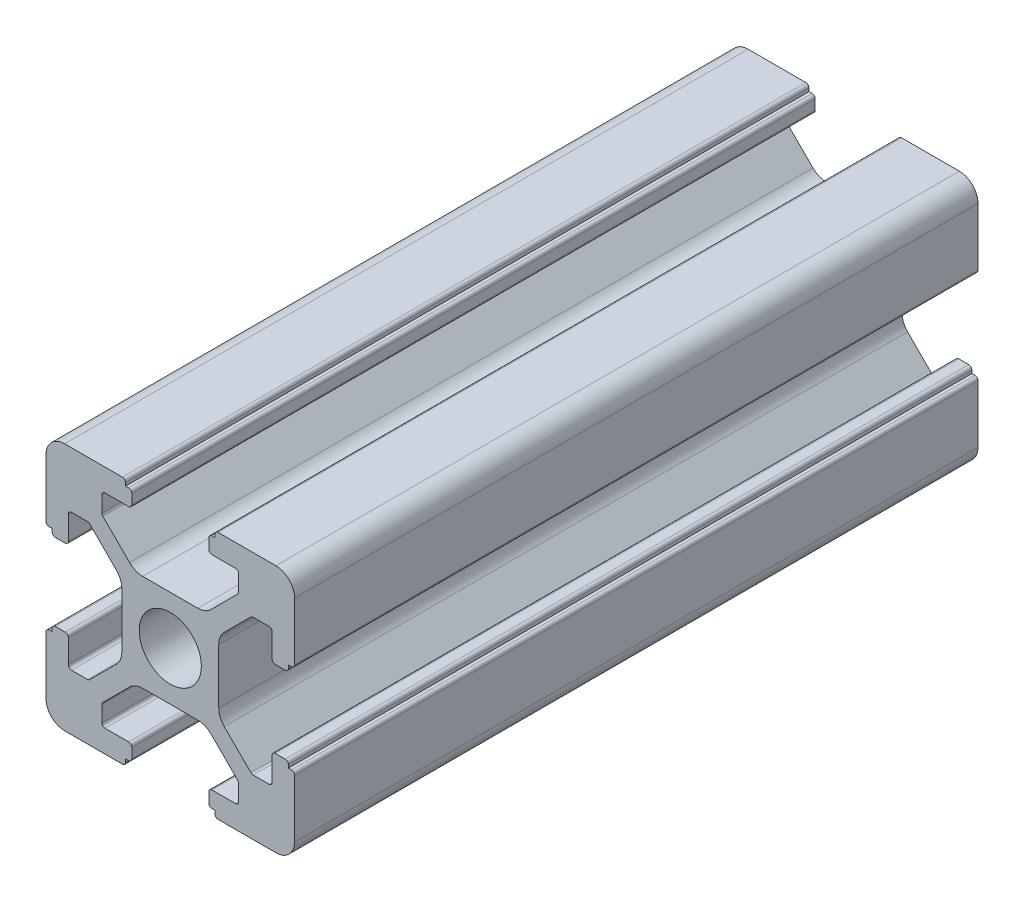
SolidWorks part; units mm, degrees
material "1060 Alloy"
ref_plane "前视基准面" through (0, 0, 0) normal (0, 0, 1) x (1, 0, 0)
ref_plane "上视基准面" through (0, 0, 0) normal (0, 1, 0) x (1, 0, 0)
ref_plane "右视基准面" through (0, 0, 0) normal (1, 0, 0) x (0, 0, -1)
sketch "草图1" plane through (0, 0, 0) normal (0, 0, 1) x (1, 0, 0)
  line L0 (0, 0) -> (0, 5.5) construction
  line L1 (-8.5023, -10.0023) -> (-3.85, -10.0023)
  line L2 (-10.0023, -8.5023) -> (-10.0023, -3.85)
  line L3 (-8.5023, 10.0023) -> (-3.85, 10.0023)
  line L4 (10.0023, -8.5023) -> (10.0023, -3.85)
  line L5 (-10.0023, -10.0023) -> (10.0023, 10.0023) construction
  line L6 (-10.0023, 10.0023) -> (10.0023, -10.0023) construction
  line L7 (-2.218, -3.9) -> (2.218, -3.9)
  line L8 (-3.9, -2.218) -> (-3.9, 2.218)
  line L9 (-2.218, 3.9) -> (2.218, 3.9)
  line L10 (3.9, -2.218) -> (3.9, 2.218)
  line L11 (-3.9, -3.9) -> (3.9, 3.9) construction
  line L12 (-3.9, 3.9) -> (3.9, -3.9) construction
  line L13 (-5.25, -8.2) -> (-3.35, -8.2)
  line L14 (-8.2, -5.25) -> (-8.2, -3.35)
  line L15 (-5.25, 8.2) -> (-3.35, 8.2)
  line L16 (8.2, -5.25) -> (8.2, -3.35)
  line L17 (-8.2, -8.2) -> (8.2, 8.2) construction
  line L18 (-8.2, 8.2) -> (8.2, -8.2) construction
  line L19 (-7.95, 5.5) -> (-6.6642, 5.5)
  line L20 (0, 0) -> (5.5, 0) construction
  line L23 (-5.5, 7.95) -> (-5.5, 6.6642)
  line L26 (0, 0) -> (-0.5303, 0.5303)
  line L27 (3.2787, 4.3393) -> (5.4268, 6.4874)
  line L28 (0, 0) -> (0.5303, -0.5303)
  line L29 (5.5, 6.6642) -> (5.5, 7.95)
  line L30 (4.3393, 3.2787) -> (6.4874, 5.4268)
  line L31 (6.6642, 5.5) -> (7.95, 5.5)
  line L32 (4.3393, -3.2787) -> (6.4874, -5.4268)
  line L33 (3.2787, -4.3393) -> (5.4268, -6.4874)
  line L34 (-3.2787, -4.3393) -> (-5.4268, -6.4874)
  line L35 (-4.3393, -3.2787) -> (-6.4874, -5.4268)
  line L36 (-4.3393, 3.2787) -> (-6.4874, 5.4268)
  line L37 (-3.2787, 4.3393) -> (-5.4268, 6.4874)
  line L38 (3.1, -8.45) -> (3.1, -9.2523)
  line L39 (8.45, 3.1) -> (9.2523, 3.1)
  line L40 (-5.5, -6.6642) -> (-5.5, -7.95)
  line L41 (-6.6642, -5.5) -> (-7.95, -5.5)
  line L42 (5.5, -6.6642) -> (5.5, -7.95)
  line L43 (6.6642, -5.5) -> (7.95, -5.5)
  line L44 (9.2523, -3.1) -> (8.45, -3.1)
  line L46 (10.0023, 3.85) -> (10.0023, 8.5023)
  line L47 (8.2, 3.35) -> (8.2, 5.25)
  line L48 (-3.1, -9.2523) -> (-3.1, -8.45)
  line L49 (-8.45, -3.1) -> (-9.2523, -3.1)
  line L50 (-9.2523, 3.1) -> (-8.45, 3.1)
  line L51 (-3.1, 8.45) -> (-3.1, 9.2523)
  line L52 (3.1, 9.2523) -> (3.1, 8.45)
  line L53 (3.85, 10.0023) -> (8.5023, 10.0023)
  line L54 (3.35, 8.2) -> (5.25, 8.2)
  line L55 (-10.0023, 3.85) -> (-10.0023, 8.5023)
  line L56 (-8.2, 3.35) -> (-8.2, 5.25)
  line L57 (3.35, -8.2) -> (5.25, -8.2)
  line L58 (3.85, -10.0023) -> (8.5023, -10.0023)
  line L59 (9.7523, -3.6) -> (9.5023, -3.6)
  line L61 (9.7523, 3.6) -> (9.5023, 3.6)
  line L62 (9.5023, -3.6) -> (9.5023, -3.35)
  line L63 (3.6, -9.7523) -> (3.6, -9.5023)
  line L64 (3.35, -9.5023) -> (3.6, -9.5023)
  line L65 (9.5023, 3.35) -> (9.5023, 3.6)
  line L66 (-3.6, -9.5023) -> (-3.35, -9.5023)
  line L67 (-3.6, -9.7523) -> (-3.6, -9.5023)
  line L68 (-9.7523, -3.6) -> (-9.5023, -3.6)
  line L69 (-9.5023, -3.35) -> (-9.5023, -3.6)
  line L70 (-9.5023, 3.6) -> (-9.5023, 3.35)
  line L71 (-9.7523, 3.6) -> (-9.5023, 3.6)
  line L72 (-3.6, 9.7523) -> (-3.6, 9.5023)
  line L73 (-3.35, 9.5023) -> (-3.6, 9.5023)
  line L74 (3.6, 9.5023) -> (3.35, 9.5023)
  line L75 (3.6, 9.7523) -> (3.6, 9.5023)
  circle A0 centre (0, 0) radius 2.5
  arc A1 (10.0023, 8.5023) -> (8.5023, 10.0023) centre (8.5023, 8.5023) ccw
  arc A2 (8.5023, -10.0023) -> (10.0023, -8.5023) centre (8.5023, -8.5023) ccw
  arc A3 (-10.0023, -8.5023) -> (-8.5023, -10.0023) centre (-8.5023, -8.5023) ccw
  arc A4 (-10.0023, 8.5023) -> (-8.5023, 10.0023) centre (-8.5023, 8.5023) cw
  arc A5 (-9.5023, -3.35) -> (-9.2523, -3.1) centre (-9.2523, -3.35) cw
  arc A6 (-9.7523, -3.6) -> (-10.0023, -3.85) centre (-9.7523, -3.85) ccw
  arc A7 (-8.45, -3.1) -> (-8.2, -3.35) centre (-8.45, -3.35) cw
  arc A8 (-7.95, -5.5) -> (-8.2, -5.25) centre (-7.95, -5.25) cw
  arc A9 (-6.4874, -5.4268) -> (-6.6642, -5.5) centre (-6.6642, -5.25) cw
  arc A10 (-5.4268, -6.4874) -> (-5.5, -6.6642) centre (-5.25, -6.6642) ccw
  arc A11 (-5.5, -7.95) -> (-5.25, -8.2) centre (-5.25, -7.95) ccw
  arc A12 (-3.6, -9.7523) -> (-3.85, -10.0023) centre (-3.85, -9.7523) cw
  arc A13 (-3.35, -9.5023) -> (-3.1, -9.2523) centre (-3.35, -9.2523) ccw
  arc A14 (-3.1, -8.45) -> (-3.35, -8.2) centre (-3.35, -8.45) ccw
  arc A15 (3.1, -8.45) -> (3.35, -8.2) centre (3.35, -8.45) cw
  arc A16 (5.5, -7.95) -> (5.25, -8.2) centre (5.25, -7.95) cw
  arc A17 (5.4268, -6.4874) -> (5.5, -6.6642) centre (5.25, -6.6642) cw
  arc A18 (6.4874, -5.4268) -> (6.6642, -5.5) centre (6.6642, -5.25) ccw
  arc A19 (7.95, -5.5) -> (8.2, -5.25) centre (7.95, -5.25) ccw
  arc A20 (8.45, -3.1) -> (8.2, -3.35) centre (8.45, -3.35) ccw
  arc A21 (9.5023, -3.35) -> (9.2523, -3.1) centre (9.2523, -3.35) ccw
  arc A22 (9.7523, -3.6) -> (10.0023, -3.85) centre (9.7523, -3.85) cw
  arc A23 (3.35, -9.5023) -> (3.1, -9.2523) centre (3.35, -9.2523) cw
  arc A24 (3.6, -9.7523) -> (3.85, -10.0023) centre (3.85, -9.7523) ccw
  arc A25 (7.95, 5.5) -> (8.2, 5.25) centre (7.95, 5.25) cw
  arc A26 (8.2, 3.35) -> (8.45, 3.1) centre (8.45, 3.35) ccw
  arc A27 (9.5023, 3.35) -> (9.2523, 3.1) centre (9.2523, 3.35) cw
  arc A28 (9.7523, 3.6) -> (10.0023, 3.85) centre (9.7523, 3.85) ccw
  arc A29 (6.6642, 5.5) -> (6.4874, 5.4268) centre (6.6642, 5.25) ccw
  arc A30 (5.4268, 6.4874) -> (5.5, 6.6642) centre (5.25, 6.6642) ccw
  arc A31 (5.5, 7.95) -> (5.25, 8.2) centre (5.25, 7.95) ccw
  arc A32 (3.1, 8.45) -> (3.35, 8.2) centre (3.35, 8.45) ccw
  arc A33 (3.6, 9.7523) -> (3.85, 10.0023) centre (3.85, 9.7523) cw
  arc A34 (3.35, 9.5023) -> (3.1, 9.2523) centre (3.35, 9.2523) ccw
  arc A35 (-9.7523, 3.6) -> (-10.0023, 3.85) centre (-9.7523, 3.85) cw
  arc A36 (-9.5023, 3.35) -> (-9.2523, 3.1) centre (-9.2523, 3.35) ccw
  arc A37 (-8.45, 3.1) -> (-8.2, 3.35) centre (-8.45, 3.35) ccw
  arc A38 (-8.2, 5.25) -> (-7.95, 5.5) centre (-7.95, 5.25) cw
  arc A39 (-6.4874, 5.4268) -> (-6.6642, 5.5) centre (-6.6642, 5.25) ccw
  arc A40 (-5.4268, 6.4874) -> (-5.5, 6.6642) centre (-5.25, 6.6642) cw
  arc A41 (-5.5, 7.95) -> (-5.25, 8.2) centre (-5.25, 7.95) cw
  arc A42 (-3.1, 8.45) -> (-3.35, 8.2) centre (-3.35, 8.45) cw
  arc A43 (-3.1, 9.2523) -> (-3.35, 9.5023) centre (-3.35, 9.2523) ccw
  arc A44 (-3.6, 9.7523) -> (-3.85, 10.0023) centre (-3.85, 9.7523) ccw
  arc A45 (-4.3393, 3.2787) -> (-3.9, 2.218) centre (-5.4, 2.218) cw
  arc A46 (-3.2787, 4.3393) -> (-2.218, 3.9) centre (-2.218, 5.4) ccw
  arc A47 (3.2787, 4.3393) -> (2.218, 3.9) centre (2.218, 5.4) cw
  arc A48 (4.3393, 3.2787) -> (3.9, 2.218) centre (5.4, 2.218) ccw
  arc A49 (4.3393, -3.2787) -> (3.9, -2.218) centre (5.4, -2.218) cw
  arc A50 (3.2787, -4.3393) -> (2.218, -3.9) centre (2.218, -5.4) ccw
  arc A51 (-4.3393, -3.2787) -> (-3.9, -2.218) centre (-5.4, -2.218) ccw
  arc A52 (-2.218, -3.9) -> (-3.2787, -4.3393) centre (-2.218, -5.4) ccw
  point P0 (0, 0)
  point P7 (10.0023, 0)
  point P62 (0, 0)
  point P76 (0, 0)
  point P92 (-8.2, -5.5)
  point P99 (0, 0)
  point P106 (-5.5, -8.2)
  point P117 (5.5, -8.2)
  point P124 (8.2, -5.5)
  point P137 (8.2, 5.5)
  point P140 (8.2, 3.1)
  point P147 (6.5607, 5.5)
  point P152 (5.5, 8.2)
  point P167 (-8.2, 5.5)
  point P174 (-5.5, 8.2)
  dimension "D1" = 1.5
  dimension "D5" = 0.25
  dimension "D6" = 1.5
  dimension "D2" = 4
  dimension "D3" = 4
  dimension "D4" = 4
extrude "凸台-拉伸1" add sketch "草图1" along normal blind 55 contours A52 L7 A50 L33 A17 L42 A16 L57 A15 L38 A23 L64 L63 A24 L58 A2 L4 A22 L59 L62 A21 L44 A20 L16 A19 L43 A18 L32 A49 L10 A48 L30 A29 L31 A25 L47 A26 L39 A27 L65 L61 A28 L46 A1 L53 A33 L75 L74 A34 L52 A32
ref_plane "Plane1" through (0, 0, 27.5) normal (0, 0, 1) x (1, 0, 0)
